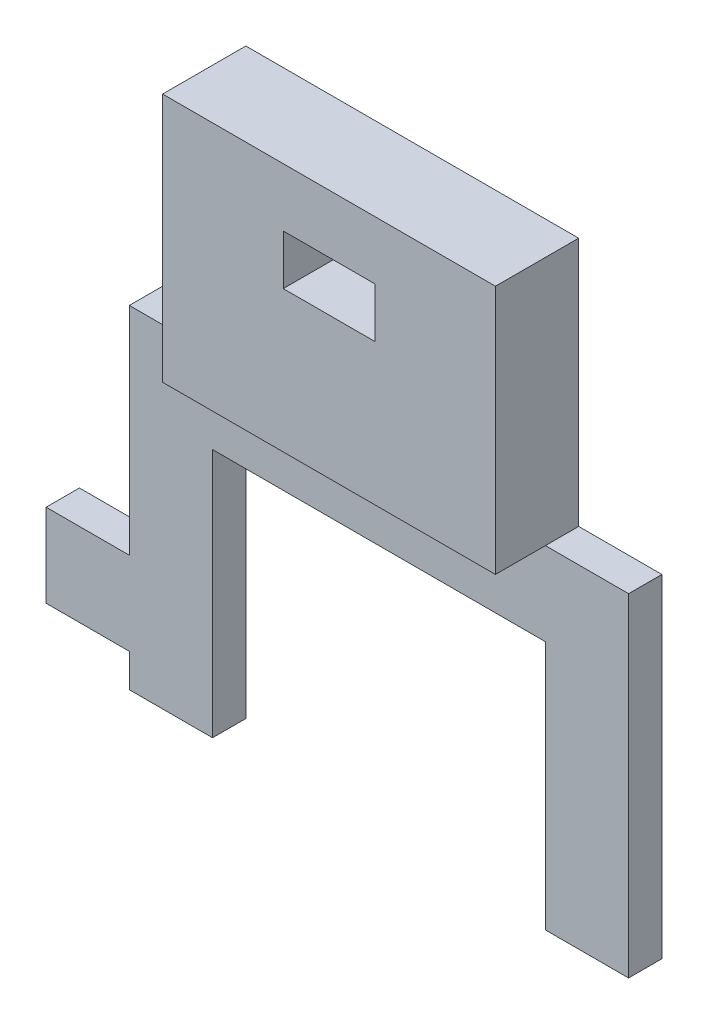
SolidWorks part; units mm, degrees
ref_plane "Přední rovina" through (0, 0, 0) normal (0, 0, 1) x (1, 0, 0)
ref_plane "Horní rovina" through (0, 0, 0) normal (0, 1, 0) x (1, 0, 0)
ref_plane "Pravá rovina" through (0, 0, 0) normal (1, 0, 0) x (0, 0, -1)
sketch "Skica1" plane through (0, 0, 0) normal (0, 0, 1) x (1, 0, 0)
  line L0 (0, 0) -> (5, 0)
  line L1 (5, 0) -> (5, -2)
  line L2 (5, -2) -> (10, -2)
  line L3 (10, -2) -> (10, 4.0825)
  line L4 (10, 4.0825) -> (10, 13)
  line L5 (10, 13) -> (30, 13)
  line L6 (30, 13) -> (30, -2)
  line L7 (30, -2) -> (35, -2)
  line L8 (35, -2) -> (35, 18)
  line L9 (35, 18) -> (5, 18)
  line L10 (5, 18) -> (5, 5)
  line L11 (5, 5) -> (0, 5)
  line L12 (0, 5) -> (0, 0)
  point P3 (2.5, 0)
  dimension "D1" = 5
  dimension "D2" = 20
  dimension "D3" = 5
  dimension "D4" = 15
  dimension "D5" = 5
  dimension "D6" = 6.0825
  dimension "D7" = 2
  dimension "D8" = 5
  dimension "D9" = 5
  dimension "D10" = 20
extrude "Přidat vysunutím1" add sketch "Skica1" along normal blind 2
sketch "Skica2" plane through (0, 18, 0) normal (0, 1, 0) x (1, 0, 0)
  line L0 (35, 0) -> (5, 0) construction
  line L1 (10, 0) -> (30, 0)
  line L2 (10, 0) -> (10, -2)
  line L3 (10, -2) -> (30, -2)
  line L4 (30, 0) -> (30, -2)
  line L5 (35, -2) -> (5, -2) construction
  line L6 (5, -2) -> (5, 0) construction
  line L7 (35, -2) -> (35, 0) construction
  dimension "D1" = 5
  dimension "D2" = 5
extrude "Přidat vysunutím2" add sketch "Skica2" along normal blind 15
sketch "Skica3" plane through (0, 0, 2) normal (0, 0, 1) x (1, 0, 0)
  line L1 (17.25, 29.5) -> (22.75, 29.5)
  line L2 (17.25, 29.5) -> (17.25, 26.5)
  line L3 (17.25, 26.5) -> (22.75, 26.5)
  line L4 (22.75, 29.5) -> (22.75, 26.5)
  line L6 (10, 18) -> (5, 18) construction
  line L7 (10, 33) -> (10, 18) construction
  point P6 (17.25, 28)
  dimension "D1" = 3
  dimension "D2" = 5.5
  dimension "D3" = 8.5
  dimension "D4" = 7.25
extrude "Odebrat vysunutím1" cut sketch "Skica3" against normal blind 15
sketch "Skica5" plane through (0, 0, 2) normal (0, 0, 1) x (1, 0, 0)
  line L0 (10, 33) -> (10, 18)
  line L1 (10, 18) -> (30, 18)
  line L2 (30, 18) -> (30, 33)
  line L3 (30, 33) -> (10, 33)
  line L4 (17.25, 29.5) -> (17.25, 26.5)
  line L5 (17.25, 26.5) -> (22.75, 26.5)
  line L6 (22.75, 26.5) -> (22.75, 29.5)
  line L7 (22.75, 29.5) -> (17.25, 29.5)
extrude "Přidat vysunutím3" add sketch "Skica5" along normal blind 3
